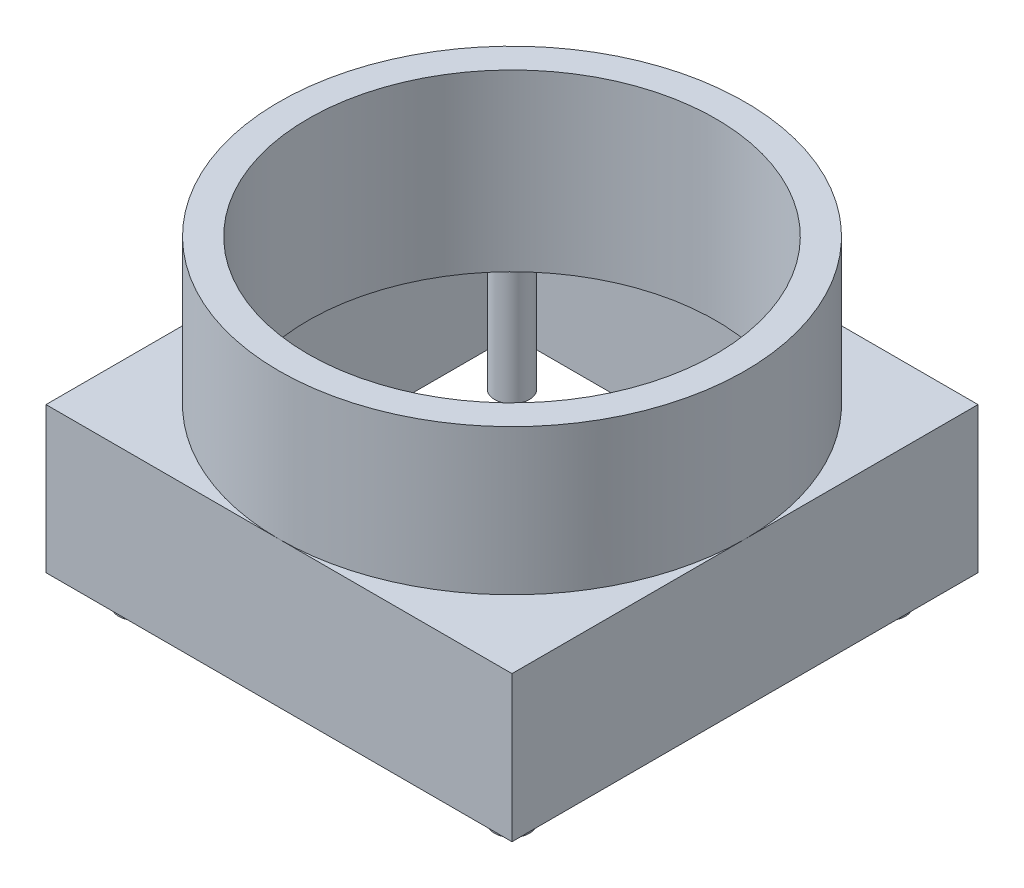
SolidWorks part; units mm, degrees
ref_plane "Front Plane" through (0, 0, 0) normal (0, 0, 1) x (1, 0, 0)
ref_plane "Top Plane" through (0, 0, 0) normal (0, 1, 0) x (1, 0, 0)
ref_plane "Right Plane" through (0, 0, 0) normal (1, 0, 0) x (0, 0, -1)
sketch "Sketch1" plane through (0, 0, 0) normal (0, 1, 0) x (1, 0, 0)
  line L1 (-3.525, 3.525) -> (3.525, 3.525)
  line L2 (-3.525, 3.525) -> (-3.525, -3.525)
  line L3 (-3.525, -3.525) -> (3.525, -3.525)
  line L4 (3.525, 3.525) -> (3.525, -3.525)
  line L5 (-4, 4) -> (4, 4)
  line L6 (-4, 4) -> (-4, -4)
  line L7 (-4, -4) -> (4, -4)
  line L8 (4, 4) -> (4, -4)
  point P9 (0, 3.525)
  point P11 (3.525, 0)
  point P12 (4, 0)
  point P13 (0, 4)
  dimension "D1" = 8
  dimension "D2" = 7.05
  dimension "D3" = 7.05
  dimension "D4" = 8
extrude "Boss-Extrude1" add sketch "Sketch1" along normal blind 2 contours L8 L5 L6 L7 L1 L4 L3 L2 | L4 L1 L2 L3
sketch "Sketch2" plane through (0, 2, 0) normal (0, 1, 0) x (1, 0, 0)
  line L4 (4, -4) -> (4, 4)
  line L5 (4, 4) -> (-4, 4)
  line L6 (-4, 4) -> (-4, -4)
  line L7 (-4, -4) -> (4, -4)
  line L8 (4, -4) -> (4, 4)
  line L9 (4, 4) -> (-4, 4)
  line L10 (-4, 4) -> (-4, -4)
  line L11 (-4, -4) -> (4, -4)
  dimension "D1" = 0
sketch "Sketch3" plane through (0, 2, 0) normal (0, 1, 0) x (1, 0, 0)
  line L4 (4, -4) -> (4, 4)
  line L5 (4, 4) -> (-4, 4)
  line L6 (-4, 4) -> (-4, -4)
  line L7 (-4, -4) -> (4, -4)
  line L8 (4, -4) -> (4, 4)
  line L9 (4, 4) -> (-4, 4)
  line L10 (-4, 4) -> (-4, -4)
  line L11 (-4, -4) -> (4, -4)
  circle A0 centre (0, 0) radius 3.5
  circle A1 centre (0, 0) radius 4
  line M11 (3.525, -3.525) -> (-3.525, -3.525)
  line M12 (-3.525, -3.525) -> (-3.525, 3.525)
  line M13 (-3.525, 3.525) -> (3.525, 3.525)
  line M14 (3.525, 3.525) -> (3.525, -3.525)
  dimension "D1" = 0
extrude "Boss-Extrude3" add sketch "Sketch3" along normal blind 3 contours A1 A0 M11 M14 M13 M12 | A1 M14 | A1 M13 | A1 M12 | A1 M11
sketch "Sketch5" plane through (0, 2, 0) normal (0, 1, 0) x (1, 0, 0)
  line L0 (0, 4) -> (-4, 4) construction
  line L1 (-4, 4) -> (-4, 0) construction
  line L2 (-3.525, 1.8906) -> (-3.525, 3.525) construction
  line L3 (-3.525, 3.525) -> (-1.8906, 3.525) construction
  line L4 (4, 0) -> (4, 4) construction
  line L5 (4, 4) -> (0, 4) construction
  line L6 (1.8906, 3.525) -> (3.525, 3.525) construction
  line L7 (3.525, 3.525) -> (3.525, 1.8906) construction
  line L8 (3.525, -1.8906) -> (3.525, -3.525) construction
  line L9 (3.525, -3.525) -> (1.8906, -3.525) construction
  line L10 (0, -4) -> (4, -4) construction
  line L11 (4, -4) -> (4, 0) construction
  line L12 (-4, 0) -> (-4, -4) construction
  line L13 (-4, -4) -> (0, -4) construction
  line L14 (-1.8906, -3.525) -> (-3.525, -3.525) construction
  line L15 (-3.525, -3.525) -> (-3.525, -1.8906) construction
  line L16 (0, 4) -> (-4, 4)
  line L17 (-4, 4) -> (-4, 0)
  line L18 (-3.525, 1.8906) -> (-3.525, 3.525)
  line L19 (-3.525, 3.525) -> (-1.8906, 3.525)
  line L20 (4, 0) -> (4, 4)
  line L21 (4, 4) -> (0, 4)
  line L22 (1.8906, 3.525) -> (3.525, 3.525)
  line L23 (3.525, 3.525) -> (3.525, 1.8906)
  line L24 (3.525, -1.8906) -> (3.525, -3.525)
  line L25 (3.525, -3.525) -> (1.8906, -3.525)
  line L26 (0, -4) -> (4, -4)
  line L27 (4, -4) -> (4, 0)
  line L28 (-4, 0) -> (-4, -4)
  line L29 (-4, -4) -> (0, -4)
  line L30 (-1.8906, -3.525) -> (-3.525, -3.525)
  line L31 (-3.525, -3.525) -> (-3.525, -1.8906)
  circle A0 centre (0, 0) radius 4 construction
  arc A1 (0, 4) -> (-1.8906, 3.525) centre (0, 0) ccw construction
  arc A2 (-3.525, 1.8906) -> (-4, 0) centre (0, 0) ccw construction
  arc A3 (4, 0) -> (3.525, 1.8906) centre (0, 0) ccw construction
  arc A4 (1.8906, 3.525) -> (0, 4) centre (0, 0) ccw construction
  arc A5 (3.525, -1.8906) -> (4, 0) centre (0, 0) ccw construction
  arc A6 (0, -4) -> (1.8906, -3.525) centre (0, 0) ccw construction
  arc A7 (-4, 0) -> (-3.525, -1.8906) centre (0, 0) ccw construction
  arc A8 (-1.8906, -3.525) -> (0, -4) centre (0, 0) ccw construction
  circle A9 centre (0, 0) radius 4
  arc A10 (0, 4) -> (-1.8906, 3.525) centre (0, 0) ccw
  arc A11 (-3.525, 1.8906) -> (-4, 0) centre (0, 0) ccw
  arc A12 (4, 0) -> (3.525, 1.8906) centre (0, 0) ccw
  arc A13 (1.8906, 3.525) -> (0, 4) centre (0, 0) ccw
  arc A14 (3.525, -1.8906) -> (4, 0) centre (0, 0) ccw
  arc A15 (0, -4) -> (1.8906, -3.525) centre (0, 0) ccw
  arc A16 (-4, 0) -> (-3.525, -1.8906) centre (0, 0) ccw
  arc A17 (-1.8906, -3.525) -> (0, -4) centre (0, 0) ccw
  arc M1 (-3.525, -1.8906) -> (-4, 0) centre (0, 0) cw
  line M2 (-4, 0) -> (-4, -4)
  line M3 (-4, -4) -> (0, -4)
  arc M4 (0, -4) -> (-1.8906, -3.525) centre (0, 0) cw
  line M5 (-1.8906, -3.525) -> (-3.525, -3.525)
  line M6 (-3.525, -3.525) -> (-3.525, -1.8906)
extrude "Boss-Extrude4" add sketch "Sketch5" along normal blind 0.5 contours A9 L20 L21 L22 L23 | A9 L26 L27 L24 L25 | M6 M1 M2 M3 M4 M5 | A9 L16 L17 L18 L19 | A9 L19 L18 | A9 M6 M5 | A9 L25 L24 | A9 L23 L22
sketch "Sketch10" plane through (0, 2, 0) normal (0, -1, 0) x (1, 0, 0)
  line L14 (-3.525, 3.525) -> (3.525, 3.525) construction
  line L15 (3.525, -3.525) -> (3.525, 3.525) construction
  line L16 (-3.525, -3.525) -> (-3.525, 3.525) construction
  line L17 (-3.525, -3.525) -> (3.525, -3.525) construction
  circle A8 centre (3.225, 3.225) radius 0.3
  circle A9 centre (3.225, -3.225) radius 0.3
  circle A10 centre (-3.225, -3.225) radius 0.3
  circle A11 centre (-3.225, 3.225) radius 0.3
  dimension "D1" = 0.6
  dimension "D2" = 0.6
  dimension "D3" = 0.6
  dimension "D4" = 0.6
extrude "Boss-Extrude6" add sketch "Sketch10" along normal blind 2.5 separate body
